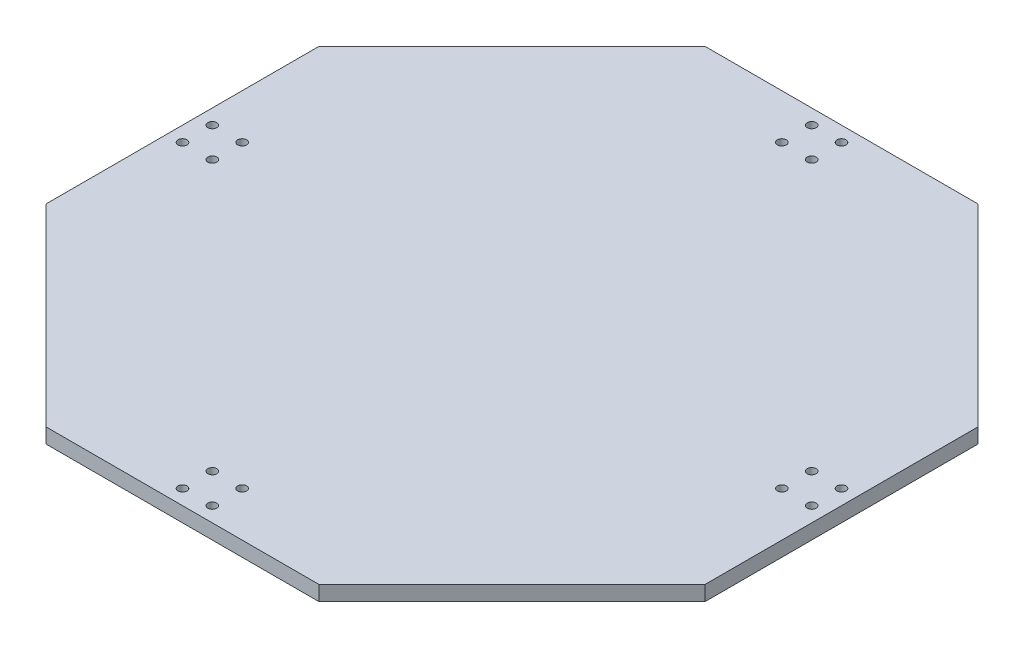
SolidWorks part; units mm, degrees
ref_plane "정면" through (0, 0, 0) normal (0, 0, 1) x (1, 0, 0)
ref_plane "윗면" through (0, 0, 0) normal (0, 1, 0) x (1, 0, 0)
ref_plane "우측면" through (0, 0, 0) normal (1, 0, 0) x (0, 0, -1)
sketch "스케치1" plane through (0, 0, 0) normal (0, 1, 0) x (1, 0, 0)
  line L0 (0, 278.2405) -> (0, -303.6506) construction
  line L1 (-342.3832, 0) -> (358.9353, 0) construction
  line L3 (45.7706, -110.5) -> (110.5, -45.7706)
  line L4 (110.5, -45.7706) -> (110.5, 45.7706)
  line L5 (110.5, 45.7706) -> (45.7706, 110.5)
  line L6 (45.7706, 110.5) -> (-45.7706, 110.5)
  line L7 (-45.7706, 110.5) -> (-110.5, 45.7706)
  line L8 (-110.5, 45.7706) -> (-110.5, -45.7706)
  line L9 (-110.5, -45.7706) -> (-45.7706, -110.5)
  line L10 (-45.7706, -110.5) -> (45.7706, -110.5)
  circle A0 centre (0, 0) radius 110.5 construction
  circle A1 centre (-5, 105.5) radius 1.5
  circle A2 centre (-5, 95.5) radius 1.5
  circle A7 centre (5, 95.5) radius 1.5
  circle A8 centre (5, 105.5) radius 1.5
  circle A9 centre (105.5, 5) radius 1.5
  circle A10 centre (95.5, 5) radius 1.5
  circle A15 centre (95.5, -5) radius 1.5
  circle A16 centre (105.5, -5) radius 1.5
  circle A17 centre (5, -105.5) radius 1.5
  circle A18 centre (5, -95.5) radius 1.5
  circle A23 centre (-5, -95.5) radius 1.5
  circle A24 centre (-5, -105.5) radius 1.5
  circle A25 centre (-105.5, -5) radius 1.5
  circle A26 centre (-95.5, -5) radius 1.5
  circle A31 centre (-95.5, 5) radius 1.5
  circle A32 centre (-105.5, 5) radius 1.5
  point P82 (0, 0)
  point P115 (0, 0)
  dimension "D2" = 3
  dimension "D5" = 3
  dimension "D1" = 221
  dimension "D3" = 5
  dimension "D4" = 5
  dimension "D6" = 10
  dimension "D11" = 4
extrude "보스-돌출1" add sketch "스케치1" along normal blind 5
